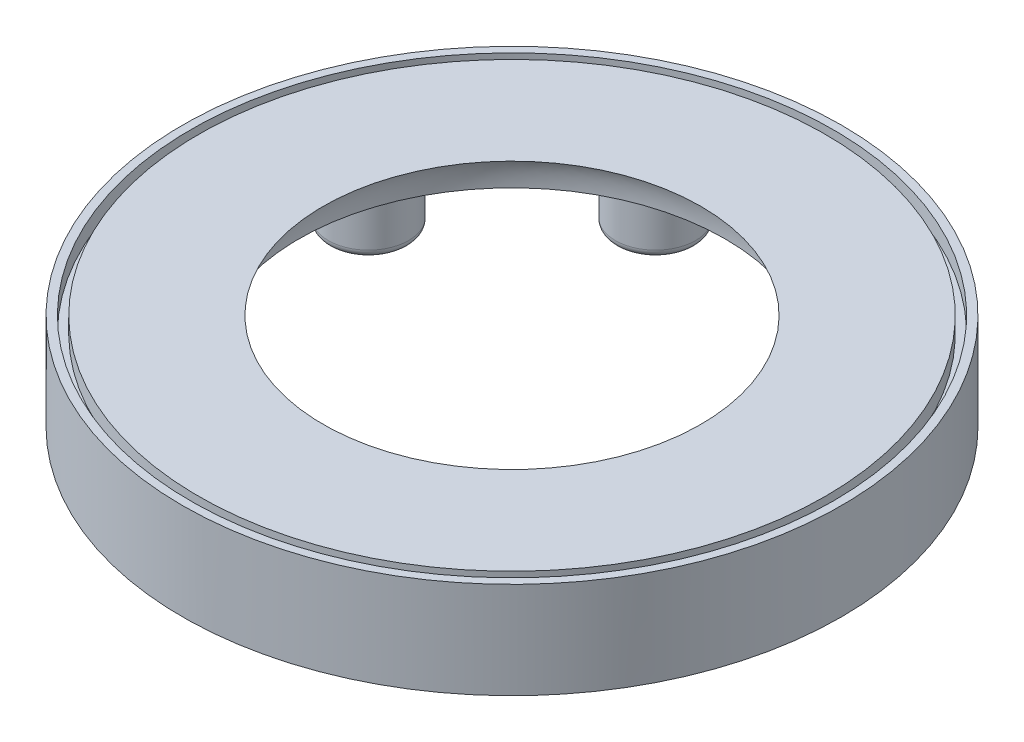
SolidWorks part; units mm, degrees
other "Markup1"
sketch "Sketch7" plane through (41, -9, -41) normal (0.3437, -0.7209, -0.6019) x (0.7608, 0.5894, -0.2715)
ref_plane "Front Plane" through (0, 0, 0) normal (0, 0, 1) x (1, 0, 0)
ref_plane "Top Plane" through (0, 0, 0) normal (0, 1, 0) x (1, 0, 0)
ref_plane "Right Plane" through (0, 0, 0) normal (1, 0, 0) x (0, 0, -1)
sketch "Sketch3" plane through (0, 0, 0) normal (0, 0, 1) x (1, 0, 0)
  line L0 (-26.5, 0) -> (-41, 0)
  line L1 (-41, 0) -> (-41, 5)
  line L2 (-41, 5) -> (-23.5, 5)
  line L3 (-26.5, 0) -> (-26.5, 5) construction
  line L4 (-26.5, 5) -> (-23.5, 5) construction
  line L5 (0, 0) -> (0, 5.246) construction
  spline S0 degree 2 poles (-26.5, 0) (-26.5, 5) (-23.5, 5) knots 0 0 0 1 1 1
  dimension "D1" = 5
  dimension "D2" = 26.5
  dimension "D3" = 23.5
  dimension "D4" = 41
revolve "Revolve1" add sketch "Sketch3" angle 360 about L5
sketch "Sketch4" plane through (0, 0, 0) normal (0, -1, 0) x (1, 0, 0)
  line L0 (-35, 0) -> (-33, 0) construction
  line L3 (-33, 1.9) -> (-33, -1.9)
  line L4 (-35, 1.9) -> (-35, -1.9)
  line L5 (1.9, 33) -> (-1.9, 33)
  line L6 (1.9, 35) -> (-1.9, 35)
  line L7 (33, -1.9) -> (33, 1.9)
  line L8 (35, -1.9) -> (35, 1.9)
  line L9 (-1.9, -33) -> (1.9, -33)
  line L10 (-1.9, -35) -> (1.9, -35)
  arc A0 (-35, 1.9) -> (-35, -1.9) centre (-35, 0) ccw
  arc A1 (-33, -1.9) -> (-33, 1.9) centre (-33, 0) ccw
  arc A2 (-1.9, 33) -> (1.9, 33) centre (0, 33) ccw
  arc A3 (1.9, 35) -> (-1.9, 35) centre (0, 35) ccw
  arc A4 (33, 1.9) -> (33, -1.9) centre (33, 0) ccw
  arc A5 (35, -1.9) -> (35, 1.9) centre (35, 0) ccw
  arc A6 (1.9, -33) -> (-1.9, -33) centre (0, -33) ccw
  arc A7 (-1.9, -35) -> (1.9, -35) centre (0, -35) ccw
  point P3 (-34, 0)
  point P29 (0, 0)
  dimension "D2" = 1.9
  dimension "D3" = 33
  dimension "D1" = 2
  dimension "D4" = 4
extrude "Boss-Extrude1" add sketch "Sketch4" along normal blind 2
fillet "Fillet1" radius 0.5 24 edges at (33, -2, 0) (31.1, -2, 0) (35, -2, 0) (36.9, -2, 0) (0, -2, -35) (0, -2, -36.9) (0, -2, -33) (0, -2, -31.1) (-33, -2, 0) (-31.1, -2, 0) (-35, -2, 0) (-36.9, -2, 0) (0, -2, 35) (0, -2, 36.9) (0, -2, 33) (0, -2, 31.1) (0, 0, 33) (0, 0, 35) (33, 0, 0) (35, 0, 0) (0, 0, -35) (0, 0, -33) (-35, 0, 0) (-33, 0, 0)
sketch "Sketch5" plane through (0, 0, 0) normal (0, -1, 0) x (1, 0, 0)
  circle A0 centre (0, 0) radius 40
  dimension "D1" = 80
extrude "Extrude-Thin1" add sketch "Sketch5" along normal blind 7 thin
sketch "Sketch13" plane through (0, 5, 0) normal (0, 1, 0) x (1, 0, 0)
  circle A0 centre (0, 0) radius 39.5
  dimension "D1" = 79
extrude "Cut-Extrude-Thin2" cut sketch "Sketch13" against normal blind 2 thin thin type mid plane wall 1
sketch "Sketch14" plane through (0, 0, 0) normal (0, -1, 0) x (1, 0, 0)
  line L0 (0, 0) -> (17.323, -41.8213) construction
  line L1 (0, 0) -> (-42.9903, -17.8072) construction
  line L2 (0, 0) -> (0, -26.5) construction
  circle A0 centre (12.6286, -30.488) radius 5
  circle A1 centre (0, 0) radius 26.5 construction
  circle A2 centre (-12.6286, -30.488) radius 5
  circle A3 centre (-30.488, -12.6286) radius 5
  circle A4 centre (-30.488, 12.6286) radius 5
  circle A5 centre (-12.6286, 30.488) radius 5
  circle A6 centre (12.6286, 30.488) radius 5
  circle A7 centre (30.488, 12.6286) radius 5
  circle A8 centre (30.488, -12.6286) radius 5
  point P26 (0, 0)
  dimension "D2" = 10
  dimension "D3" = 33
  dimension "D1" = 22.5
  dimension "D4" = 8
extrude "Boss-Extrude2" add sketch "Sketch14" along normal blind 7
sketch "Sketch15" plane through (0, -7, 0) normal (0, -1, 0) x (1, 0, 0)
  circle A0 centre (-12.6286, -30.488) radius 3
  circle A1 centre (-30.488, -12.6286) radius 3
  circle A2 centre (-30.488, 12.6286) radius 3
  circle A3 centre (-12.6286, 30.488) radius 3
  circle A4 centre (12.6286, 30.488) radius 3
  circle A5 centre (30.488, 12.6286) radius 3
  circle A6 centre (30.488, -12.6286) radius 3
  circle A7 centre (12.6286, -30.488) radius 3
  point P19 (0, 0)
  dimension "D1" = 6
  dimension "D2" = 8
extrude "Cut-Extrude1" cut sketch "Sketch15" against normal blind 3
fillet "Fillet2" radius 1 16 edges at (-12.6286, -7, -35.488) (-12.6286, 0, -25.488) (12.6286, 0, -25.488) (12.6286, -7, -35.488) (30.488, 0, -7.6286) (30.488, -7, -17.6286) (30.488, 0, 17.6286) (30.488, -7, 7.6286) (12.6286, 0, 35.488) (12.6286, -7, 25.488) (-12.6286, 0, 35.488) (-12.6286, -7, 25.488) (-30.488, 0, 17.6286) (-30.488, -7, 7.6286) (-30.488, -7, -17.6286) (-30.488, 0, -7.6286)
